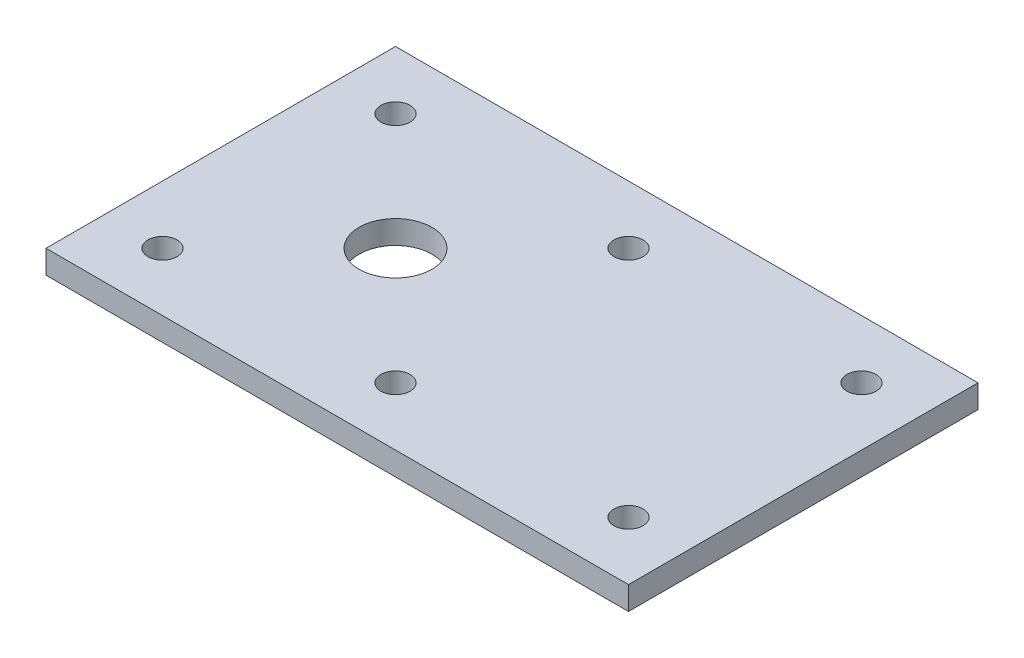
SolidWorks part; units mm, degrees
ref_plane "Front Plane" through (0, 0, 0) normal (0, 0, 1) x (1, 0, 0)
ref_plane "Top Plane" through (0, 0, 0) normal (0, 1, 0) x (1, 0, 0)
ref_plane "Right Plane" through (0, 0, 0) normal (1, 0, 0) x (0, 0, -1)
sketch "Sketch1" plane through (0, 0, 0) normal (0, 1, 0) x (1, 0, 0)
  line L0 (-60, 0) -> (140, 0) construction
  line L1 (-60, -60) -> (140, -60)
  line L2 (-60, -60) -> (-60, 60)
  line L3 (-60, 60) -> (140, 60)
  line L4 (140, -60) -> (140, 60)
  dimension "D1" = 200
  dimension "D2" = 120
  dimension "D3" = 60
extrude "Boss-Extrude1" add sketch "Sketch1" along normal blind 8
sketch "Sketch2" plane through (0, 8, 0) normal (0, 1, 0) x (1, 0, 0)
  line L0 (-60, 60) -> (-60, -60) construction
  line L1 (140, 60) -> (-60, 60) construction
  circle A0 centre (-40, 40) radius 5
  dimension "D1" = 20
  dimension "D3" = 10
  dimension "D2" = 20
extrude "Cut-Extrude1" cut sketch "Sketch2" against normal through all
pattern_linear "LPattern1" count 2 spacing 80 along (0, 0, 1) count 3 spacing 80 along (1, 0, 0) of "Cut-Extrude1"
sketch "Sketch3" plane through (0, 8, 0) normal (0, 1, 0) x (1, 0, 0)
  circle A0 centre (0, 0) radius 12.5
  dimension "D1" = 25
extrude "Cut-Extrude2" cut sketch "Sketch3" against normal through all
